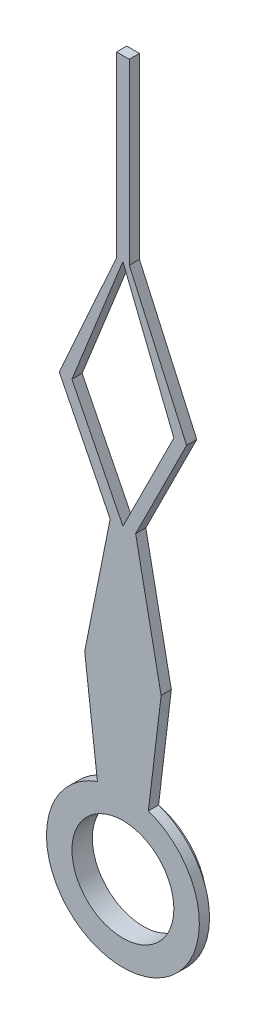
SolidWorks part; units mm, degrees
ref_plane "Front Plane" through (0, 0, 0) normal (0, 0, 1) x (1, 0, 0)
ref_plane "Top Plane" through (0, 0, 0) normal (0, 1, 0) x (1, 0, 0)
ref_plane "Right Plane" through (0, 0, 0) normal (1, 0, 0) x (0, 0, -1)
sketch "Croquis1" plane through (0, 0, 0) normal (0, 0, 1) x (1, 0, 0)
  line L0 (0.5, 1.4142) -> (0.75, 3.5)
  line L1 (-0.5, 1.4142) -> (-0.75, 3.5)
  line L2 (0.75, 3.5) -> (0.25, 6)
  line L3 (-0.75, 3.5) -> (-0.25, 6)
  line L4 (-0.25, 6) -> (-1.25, 8)
  line L5 (0.25, 6) -> (1.25, 8)
  line L6 (0, 6) -> (1, 8)
  line L7 (0, 6) -> (-1, 8)
  line L9 (-1, 8) -> (0, 10.5)
  line L10 (0, 10.5) -> (1, 8)
  line L11 (1.25, 8) -> (0.125, 10.5)
  line L12 (-1.25, 8) -> (-0.125, 10.5)
  line L13 (-0.125, 10.5) -> (-0.125, 14)
  line L14 (-0.125, 14) -> (0.125, 14)
  line L15 (0.125, 14) -> (0.125, 10.5)
  circle A0 centre (0, 0) radius 1
  arc A1 (-0.5, 1.4142) -> (0.5, 1.4142) centre (0, 0) ccw
  dimension "D4" = 1.5
  dimension "D19" = 2
  dimension "D2" = 0.5
  dimension "D3" = 2.5
  dimension "D5" = 3.5
  dimension "D6" = 0.75
  dimension "D7" = 0.75
  dimension "D8" = 0.25
  dimension "D9" = 0.25
  dimension "D10" = 1
  dimension "D11" = 1
  dimension "D12" = 2
  dimension "D13" = 0.25
  dimension "D14" = 0.25
  dimension "D15" = 2.5
  dimension "D16" = 0.125
  dimension "D17" = 0.125
  dimension "D18" = 3.5
extrude "Saliente-Extruir1" add sketch "Croquis1" along normal blind 0.2
sketch "Croquis2" plane through (0, 0, 0) normal (0, 0, -1) x (-1, 0, 0)
  circle A0 centre (0, 0) radius 1.25
  circle A1 centre (0, 0) radius 1 construction
  circle A2 centre (0, 0) radius 1
  dimension "D1" = 2.5
extrude "Saliente-Extruir2" add sketch "Croquis2" along normal blind 0.2
